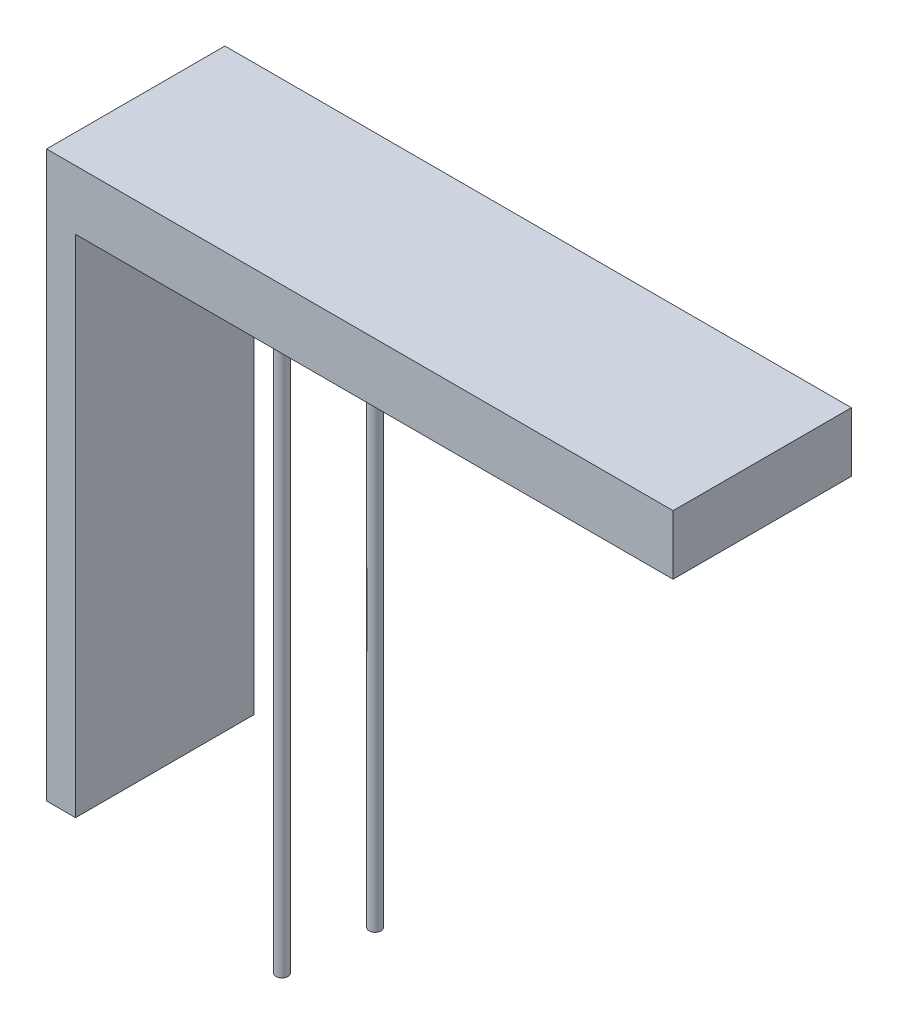
SolidWorks part; units mm, degrees
material "ABS"
ref_plane "Plan de face" through (0, 0, 0) normal (0, 0, 1) x (1, 0, 0)
ref_plane "Plan de dessus" through (0, 0, 0) normal (0, 1, 0) x (1, 0, 0)
ref_plane "Plan de droite" through (0, 0, 0) normal (1, 0, 0) x (0, 0, -1)
sketch "Esquisse1" plane through (0, 0, 0) normal (0, 0, 1) x (1, 0, 0)
  line L0 (123.7337, 14.5) -> (123.7337, 31.5)
  line L1 (149.4181, 31.5) -> (119.4663, 31.5) construction
  line L2 (123.7337, 14.5) -> (122.7596, 14.5)
  line L3 (122.7596, 14.5) -> (122.7596, 33.5)
  line L4 (123.7337, 31.5) -> (143.8385, 31.5)
  line L5 (143.8385, 31.5) -> (143.8385, 33.5)
  line L6 (143.8385, 33.5) -> (122.7596, 33.5)
  line L7 (149.4181, 33.5) -> (119.4663, 33.5) construction
  line L8 (123.7337, 22.249) -> (123.7337, 20.153) construction
  line L9 (119.4663, 14.5) -> (129.4663, 14.5) construction
  arc A0 (121.7596, 23) -> (121.7596, 27) centre (120.2596, 25) ccw construction
extrude "Extrusion1" add sketch "Esquisse1" along normal blind 6
sketch "Esquisse2" plane through (0, 31.5, 0) normal (0, -1, 0) x (1, 0, 0)
  circle A0 centre (128.7354, 4.0567) radius 0.2
  circle A1 centre (128.9716, 1.1591) radius 0.2
  dimension "D1" = 0.4
  dimension "D2" = 0.4
extrude "Extrusion2" add sketch "Esquisse2" along normal blind 20
